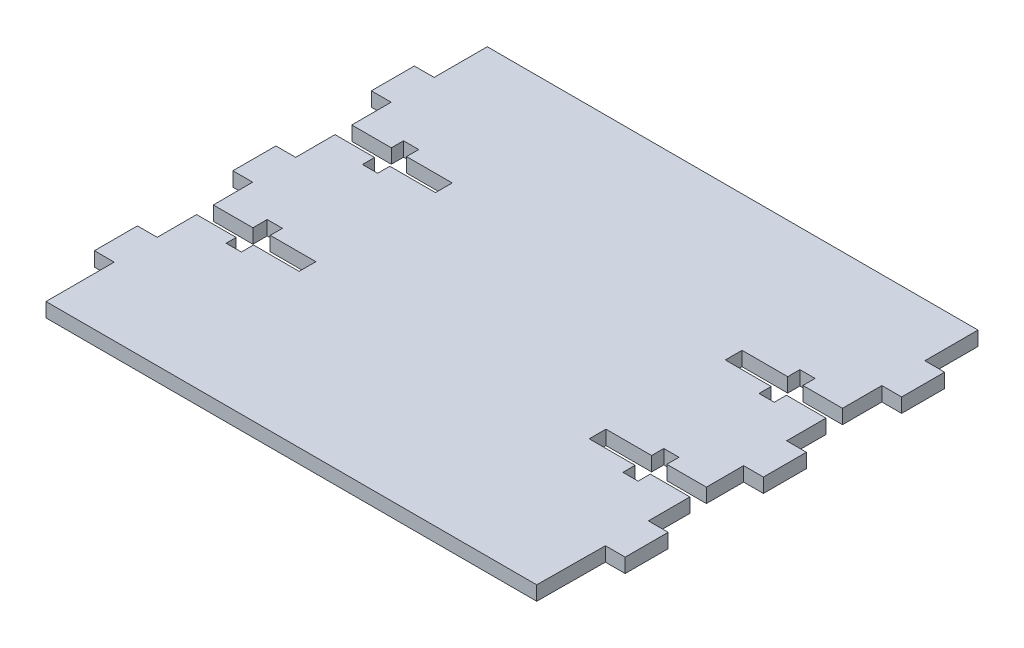
SolidWorks part; units mm, degrees
ref_plane "Front Plane" through (0, 0, 0) normal (0, 0, 1) x (1, 0, 0)
ref_plane "Top Plane" through (0, 0, 0) normal (0, 1, 0) x (1, 0, 0)
ref_plane "Right Plane" through (0, 0, 0) normal (1, 0, 0) x (0, 0, -1)
sketch "Sketch1" plane through (0, 0, 0) normal (0, 1, 0) x (1, 0, 0)
  line L1 (0, 73.66) -> (81.915, 73.66)
  line L3 (81.915, 0) -> (0, 0)
  line L5 (-3.302, 38.0166) -> (-3.302, 41.6745)
  line L6 (-3.302, 41.6745) -> (0, 41.6745)
  line L7 (-3.302, 38.0166) -> (-3.302, 34.499)
  line L8 (-3.302, 34.499) -> (0.0035, 34.499)
  line L10 (0, 48.2467) -> (0, 41.6745)
  line L11 (16.764, 48.2467) -> (16.764, 51.0407)
  line L12 (0, 48.2467) -> (6.604, 48.2467)
  line L13 (6.604, 48.2467) -> (6.604, 46.2147)
  line L14 (6.604, 46.2147) -> (9.144, 46.2147)
  line L15 (9.144, 46.2147) -> (9.144, 48.2467)
  line L16 (9.144, 48.2467) -> (16.764, 48.2467)
  line L17 (16.764, 51.0407) -> (9.144, 51.0407)
  line L18 (9.144, 51.0407) -> (9.144, 53.0727)
  line L19 (9.144, 53.0727) -> (6.604, 53.0727)
  line L20 (6.604, 53.0727) -> (6.604, 51.0407)
  line L21 (6.604, 51.0407) -> (0, 51.0407)
  line L23 (0.0035, 27.9267) -> (6.6075, 27.9267)
  line L24 (0.0035, 34.499) -> (0.0035, 27.9267)
  line L25 (6.6075, 27.9267) -> (6.6075, 30.313)
  line L26 (6.6075, 30.313) -> (9.1509, 30.313)
  line L27 (9.1509, 30.313) -> (9.1509, 28.281)
  line L28 (9.1509, 28.281) -> (16.7709, 28.281)
  line L29 (16.7709, 28.281) -> (16.7709, 25.487)
  line L30 (16.7709, 25.487) -> (9.1509, 25.487)
  line L31 (9.1509, 25.487) -> (9.1509, 23.455)
  line L32 (9.1509, 23.455) -> (6.6109, 23.455)
  line L33 (6.6109, 23.455) -> (6.6109, 25.1327)
  line L34 (6.6109, 25.1327) -> (0.0035, 25.1327)
  line L36 (0.0035, 25.1327) -> (0.0035, 18.5605)
  line L37 (0.0035, 18.5605) -> (-3.302, 18.5605)
  line L38 (-3.302, 18.5605) -> (-3.302, 11.385)
  line L39 (-3.302, 11.385) -> (0, 11.385)
  line L40 (0, 11.385) -> (0, 0)
  line L41 (0, 51.0407) -> (0, 57.613)
  line L42 (0, 57.613) -> (-3.302, 57.613)
  line L43 (-3.302, 57.613) -> (-3.302, 64.7885)
  line L44 (-3.302, 64.7885) -> (0, 64.7885)
  line L45 (0, 64.7885) -> (0, 73.66)
  line L46 (81.915, 73.66) -> (81.915, 64.7885)
  line L47 (81.915, 64.7885) -> (85.217, 64.7885)
  line L48 (85.217, 64.7885) -> (85.217, 57.613)
  line L49 (85.217, 57.613) -> (81.915, 57.613)
  line L50 (81.915, 57.613) -> (81.915, 51.0407)
  line L51 (81.915, 51.0407) -> (75.311, 51.0407)
  line L52 (75.311, 51.0407) -> (75.311, 53.0727)
  line L53 (75.311, 53.0727) -> (72.771, 53.0727)
  line L54 (72.771, 53.0727) -> (72.771, 51.0407)
  line L55 (72.771, 51.0407) -> (65.151, 51.0407)
  line L56 (65.151, 51.0407) -> (65.151, 48.2467)
  line L57 (65.151, 48.2467) -> (72.8093, 48.2467)
  line L58 (72.8093, 48.2467) -> (72.8093, 46.2147)
  line L59 (72.8093, 46.2147) -> (75.3493, 46.2147)
  line L60 (75.3493, 46.2147) -> (75.3493, 48.2467)
  line L61 (75.3493, 48.2467) -> (81.9533, 48.2467)
  line L62 (81.9533, 48.2467) -> (81.9533, 41.6745)
  line L63 (81.9533, 41.6745) -> (85.2553, 41.6745)
  line L64 (85.2553, 41.6745) -> (85.2553, 34.499)
  line L65 (85.2553, 34.499) -> (81.9533, 34.499)
  line L66 (65.1893, 26.884) -> (65.1893, 25.487)
  line L67 (65.1893, 26.884) -> (65.1893, 28.281)
  line L68 (65.1893, 28.281) -> (72.8093, 28.281)
  line L69 (72.8093, 28.281) -> (72.8093, 30.313)
  line L70 (72.8093, 30.313) -> (75.3493, 30.313)
  line L71 (75.3493, 30.313) -> (75.3493, 28.281)
  line L72 (75.3493, 28.281) -> (81.9533, 28.281)
  line L73 (81.9533, 28.281) -> (81.9533, 34.499)
  line L74 (65.1893, 25.487) -> (72.8475, 25.487)
  line L75 (72.8475, 25.487) -> (72.8475, 23.455)
  line L76 (72.8475, 23.455) -> (75.3875, 23.455)
  line L77 (75.3875, 23.455) -> (75.3875, 25.487)
  line L78 (75.3875, 25.487) -> (81.9915, 25.487)
  line L79 (81.9915, 25.487) -> (81.9915, 18.5605)
  line L80 (81.9915, 18.5605) -> (85.2935, 18.5605)
  line L81 (85.2935, 18.5605) -> (85.2935, 11.385)
  line L82 (85.2935, 11.385) -> (81.9915, 11.385)
  line L83 (81.9915, 11.385) -> (81.915, 0)
  dimension "D1" = 73.66
  dimension "D2" = 81.915
  dimension "D3" = 7.1755
  dimension "D4" = 6.5723
  dimension "D5" = 6.604
  dimension "D6" = 2.032
  dimension "D7" = 2.032
  dimension "D8" = 2.54
  dimension "D9" = 2.794
  dimension "D10" = 2.54
  dimension "D11" = 2.032
  dimension "D12" = 7.62
  dimension "D13" = 7.62
  dimension "D14" = 6.604
  dimension "D15" = 2.032
  dimension "D16" = 6.5722
  dimension "D17" = 6.604
  dimension "D18" = 2.032
  dimension "D19" = 7.62
  dimension "D20" = 2.794
  dimension "D21" = 2.032
  dimension "D22" = 6.5722
  dimension "D23" = 3.302
  dimension "D24" = 3.302
  dimension "D25" = 7.1755
  dimension "D26" = 6.5722
  dimension "D27" = 7.1755
  dimension "D28" = 2.794
  dimension "D29" = 8.8715
  dimension "D30" = 11.385
  dimension "D31" = 3.302
  dimension "D32" = 7.1755
  dimension "D33" = 6.5723
  dimension "D34" = 6.604
  dimension "D35" = 2.032
  dimension "D36" = 2.032
  dimension "D37" = 2.54
  dimension "D38" = 7.62
  dimension "D39" = 2.794
  dimension "D40" = 2.032
  dimension "D41" = 2.032
  dimension "D42" = 2.54
  dimension "D43" = 6.604
  dimension "D44" = 6.5722
  dimension "D45" = 7.62
  dimension "D46" = 3.302
  dimension "D47" = 3.302
  dimension "D48" = 3.302
  dimension "D49" = 3.302
  dimension "D50" = 7.1755
  dimension "D51" = 2.794
extrude "Boss-Extrude2" add sketch "Sketch1" against normal blind 2.3813
